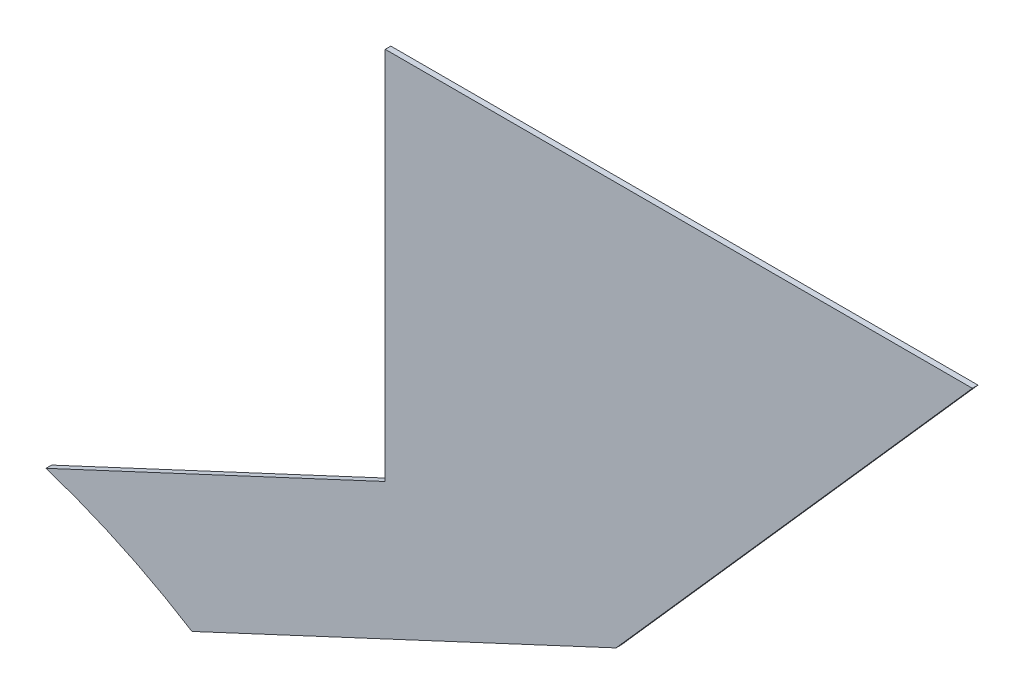
SolidWorks part; units mm, degrees
material "Plain Carbon Steel"
ref_plane "Front Plane" through (0, 0, 0) normal (0, 0, 1) x (1, 0, 0)
ref_plane "Top Plane" through (0, 0, 0) normal (0, 1, 0) x (1, 0, 0)
ref_plane "Right Plane" through (0, 0, 0) normal (1, 0, 0) x (0, 0, -1)
sketch "Sketch1" plane through (0, 0, 0) normal (0, 0, 1) x (1, 0, 0)
  line L0 (55.6311, 170.4713) -> (147.712, 213.4093)
  line L4 (210.3511, 205.6025) -> (95.25, 151.93)
  line L5 (55.6311, 170.4713) -> (55.6311, 0) construction
  line L6 (147.712, 213.4093) -> (147.712, 315.0093)
  line L7 (147.712, 315.0093) -> (307.1021, 315.0093)
  line L8 (307.1021, 315.0093) -> (210.3511, 205.6025)
  line L9 (95.25, 151.93) -> (95.25, -7.2579) construction
  circle A0 centre (0, 0) radius 179.3189 construction
  arc A1 (95.25, 151.93) -> (55.6311, 170.4713) centre (0, 0) ccw
  dimension "D1" = 358.6378
  dimension "D2" = 55.6311
  dimension "D3" = 39.6189
  dimension "D4" = 101.6
  dimension "D5" = 101.6
  dimension "D6" = 146.05
  dimension "D7" = 127
  dimension "D8" = 115
extrude "Boss-Extrude1" add sketch "Sketch1" along normal blind 1.5189
